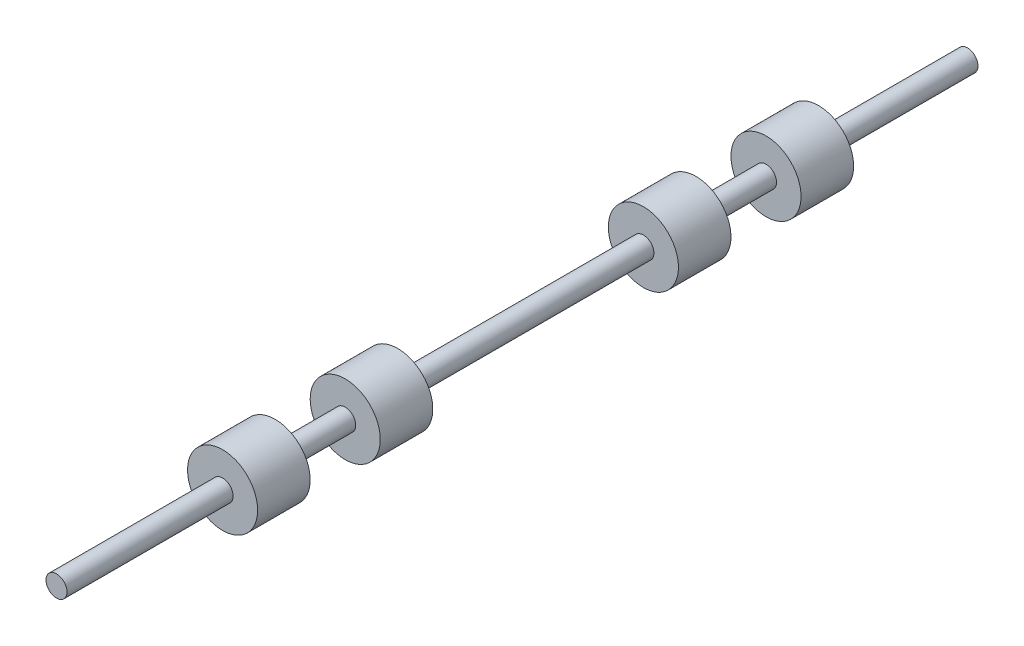
SolidWorks part; units mm, degrees
ref_plane "Front Plane" through (0, 0, 0) normal (0, 0, 1) x (1, 0, 0)
ref_plane "Top Plane" through (0, 0, 0) normal (0, 1, 0) x (1, 0, 0)
ref_plane "Right Plane" through (0, 0, 0) normal (1, 0, 0) x (0, 0, -1)
sketch "Sketch1" plane through (0, 0, 0) normal (0, 0, 1) x (1, 0, 0)
  circle A0 centre (0, 0) radius 0.3
  dimension "D1" = 0.6
extrude "Boss-Extrude1" add sketch "Sketch1" along normal blind 26
sketch "Sketch2" plane through (0, 0, 0) normal (0, 1, 0) x (1, 0, 0)
  line L0 (0, 0) -> (0, -26) construction
  line L1 (-0.3, -26) -> (0.3, -26) construction
  line L2 (0, -6.75) -> (4.7788, -6.75) construction
  line L3 (0, -4.25) -> (1, -4.25)
  line L4 (0, -4.25) -> (0, -5.75)
  line L5 (0, -5.75) -> (1, -5.75)
  line L6 (1, -4.25) -> (1, -5.75)
  line L7 (0, -4.25) -> (1, -5.75) construction
  line L8 (0, -5.75) -> (1, -4.25) construction
  line L9 (0, -7.75) -> (1, -7.75)
  line L10 (0, -7.75) -> (0, -9.25)
  line L11 (0, -9.25) -> (1, -9.25)
  line L12 (1, -7.75) -> (1, -9.25)
  line L13 (0, -7.75) -> (1, -9.25) construction
  line L14 (0, -9.25) -> (1, -7.75) construction
  line L15 (0, -18.76) -> (6.9819, -18.76) construction
  line L16 (0, -16.26) -> (1, -16.26)
  line L17 (0, -16.26) -> (0, -17.76)
  line L18 (0, -17.76) -> (1, -17.76)
  line L19 (1, -16.26) -> (1, -17.76)
  line L20 (0, -16.26) -> (1, -17.76) construction
  line L21 (0, -17.76) -> (1, -16.26) construction
  line L22 (0, -19.76) -> (1, -19.76)
  line L23 (0, -19.76) -> (0, -21.26)
  line L24 (0, -21.26) -> (1, -21.26)
  line L25 (1, -19.76) -> (1, -21.26)
  line L26 (0, -19.76) -> (1, -21.26) construction
  line L27 (0, -21.26) -> (1, -19.76) construction
  point P9 (0.5, -5)
  point P14 (0.5, -8.5)
  point P21 (0.5, -17.01)
  point P26 (0.5, -20.51)
  dimension "D1" = 1.5
  dimension "D2" = 1.5
  dimension "D3" = 1
  dimension "D4" = 1
  dimension "D5" = 2
  dimension "D6" = 1
  dimension "D7" = 1.5
  dimension "D8" = 1.5
  dimension "D9" = 1
  dimension "D10" = 2
  dimension "D11" = 12.01
  dimension "D12" = 7.24
revolve "Revolve1" add sketch "Sketch2" angle 360 about L0
